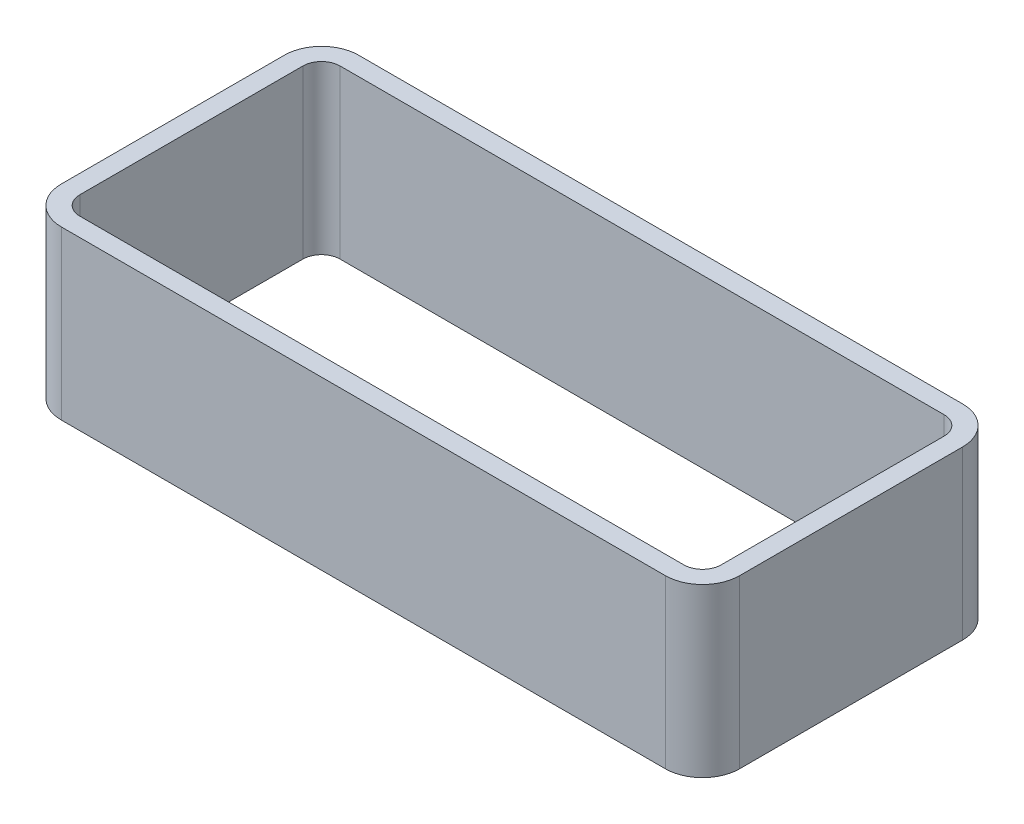
SolidWorks part; units mm, degrees
ref_plane "Front Plane" through (0, 0, 0) normal (0, 0, 1) x (1, 0, 0)
ref_plane "Top Plane" through (0, 0, 0) normal (0, 1, 0) x (1, 0, 0)
ref_plane "Right Plane" through (0, 0, 0) normal (1, 0, 0) x (0, 0, -1)
sketch "Sketch1" plane through (0, 0, 0) normal (0, 1, 0) x (1, 0, 0)
  line L0 (-36.5, -12) -> (-36.5, 12)
  line L1 (-32.5, -14) -> (32.5, -14)
  line L2 (-34.5, -12) -> (-34.5, 12)
  line L3 (-32.5, 14) -> (32.5, 14)
  line L4 (34.5, -12) -> (34.5, 12)
  line L5 (-34.5, -14) -> (34.5, 14) construction
  line L6 (-34.5, 14) -> (34.5, -14) construction
  line L7 (-32.5, 16) -> (32.5, 16)
  line L8 (36.5, -12) -> (36.5, 12)
  line L9 (-32.5, -16) -> (32.5, -16)
  arc A0 (-32.5, 14) -> (-34.5, 12) centre (-32.5, 12) ccw
  arc A1 (34.5, 12) -> (32.5, 14) centre (32.5, 12) ccw
  arc A2 (-32.5, -14) -> (-34.5, -12) centre (-32.5, -12) cw
  arc A3 (34.5, -12) -> (32.5, -14) centre (32.5, -12) cw
  arc A4 (-32.5, 16) -> (-36.5, 12) centre (-32.5, 12) ccw
  arc A5 (36.5, 12) -> (32.5, 16) centre (32.5, 12) ccw
  arc A6 (36.5, -12) -> (32.5, -16) centre (32.5, -12) cw
  arc A7 (-32.5, -16) -> (-36.5, -12) centre (-32.5, -12) cw
  point P0 (0, 0)
  dimension "D3" = 2
  dimension "D4" = 2
  dimension "D5" = 2
  dimension "D6" = 2
  dimension "D1" = 69
  dimension "D2" = 28
  dimension "D7" = 2
extrude "Boss-Extrude2" add sketch "Sketch1" along normal blind 18
